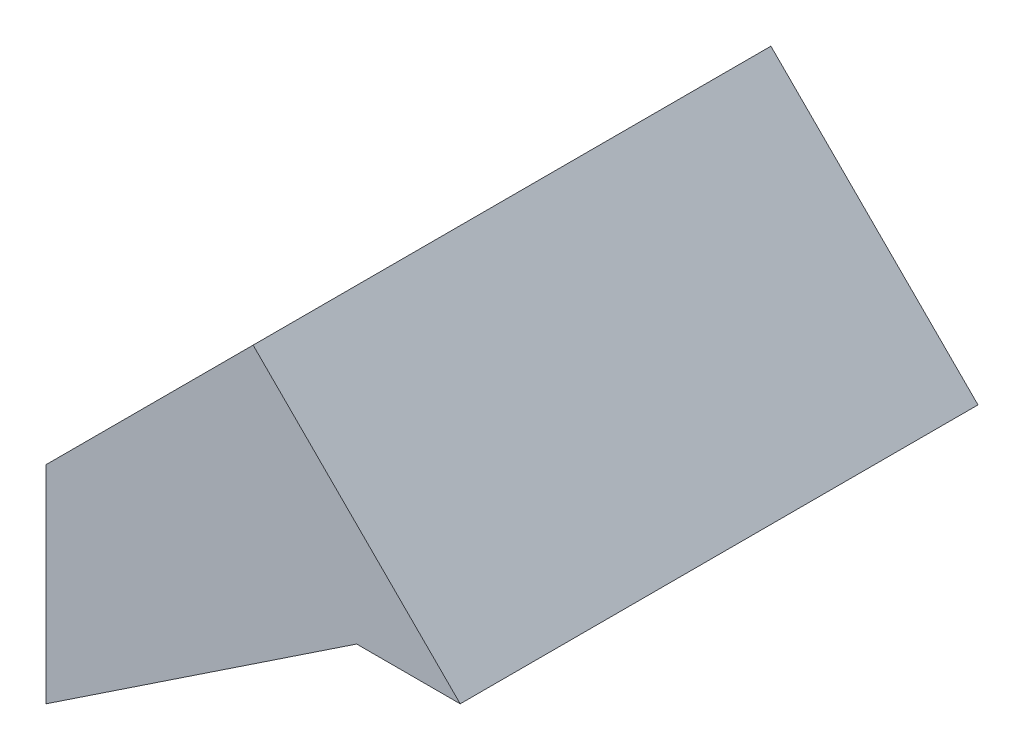
SolidWorks part; units mm, degrees
ref_plane "Front Plane" through (0, 0, 0) normal (0, 0, 1) x (1, 0, 0)
ref_plane "Top Plane" through (0, 0, 0) normal (0, 1, 0) x (1, 0, 0)
ref_plane "Right Plane" through (0, 0, 0) normal (1, 0, 0) x (0, 0, -1)
sketch "Sketch1" plane through (0, 0, 0) normal (0, 0, 1) x (1, 0, 0)
  line L0 (-20, 0) -> (-10, 10)
  line L1 (-10, 10) -> (0, 0)
  line L2 (0, 0) -> (-5, 0)
  line L3 (-5, 0) -> (-20, -10)
  line L4 (-20, -10) -> (-20, 0)
  dimension "D1" = 5
  dimension "D2" = 10
  dimension "D3" = 15
  dimension "D4" = 10
  dimension "D5" = 10
extrude "Boss-Extrude1" add sketch "Sketch1" along normal blind 25
